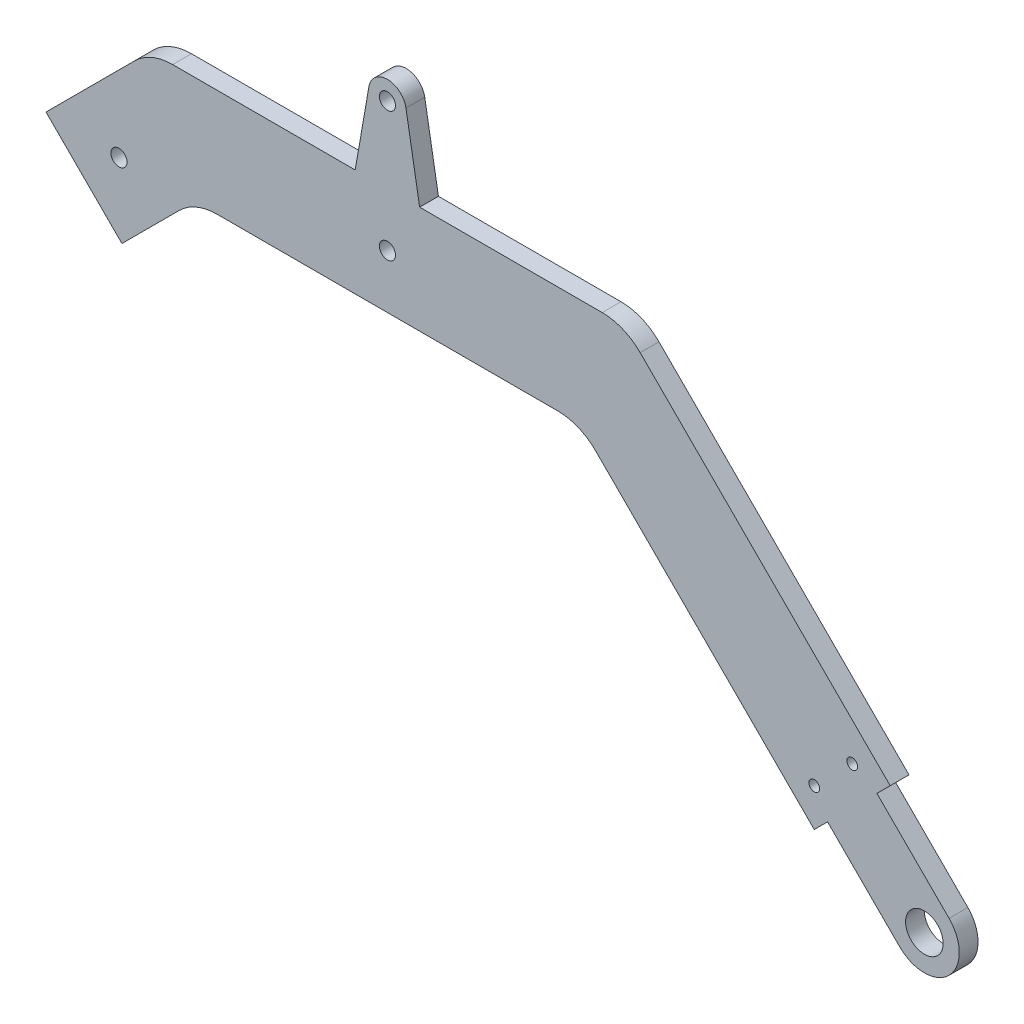
SolidWorks part; units mm, degrees
ref_plane "Front Plane" through (0, 0, 0) normal (0, 0, 1) x (1, 0, 0)
ref_plane "Top Plane" through (0, 0, 0) normal (0, 1, 0) x (1, 0, 0)
ref_plane "Right Plane" through (0, 0, 0) normal (1, 0, 0) x (0, 0, -1)
sketch "Sketch1" plane through (0, 0, 0) normal (0, 0, 1) x (1, 0, 0)
  line L0 (100, 0) -> (-100, 0)
  line L3 (-100, 0) -> (0, 100) construction
  line L4 (0, 100) -> (100, 0) construction
  line L5 (0, 0) -> (-50, 50) construction
  line L7 (0, 100) -> (0, 60) construction
  line L9 (-40, 60) -> (40, 60) construction
  circle A0 centre (-100, 0) radius 20
  circle A1 centre (0, 0) radius 20
  circle A2 centre (100, 0) radius 19.9987
  point P4 (0, 0)
  dimension "D5" = 40
  dimension "D6" = 39.9975
  dimension "D1" = 200
  dimension "D2" = 90
  dimension "D3" = 90
  dimension "D4" = 80
  dimension "D7" = 141.4214
  dimension "D8" = 70.7107
sketch "Sketch2" plane through (0, 0, 0) normal (0, 0, 1) x (1, 0, 0)
  line L0 (-56.5165, 43.4835) -> (-40, 60) construction
  line L1 (-100, 0) -> (0, 100) construction
  line L2 (-40, 60) -> (40, 60) construction
  line L3 (40, 60) -> (86.565, 13.435) construction
  line L4 (0, 100) -> (100, 0) construction
  line L5 (-49.4454, 36.4124) -> (-35.8579, 50)
  line L6 (-35.8579, 50) -> (35.8579, 50)
  line L7 (35.8579, 50) -> (79.4939, 6.364)
  line L8 (-63.5876, 50.5546) -> (-44.1421, 70)
  line L9 (-44.1421, 70) -> (44.1421, 70)
  line L10 (44.1421, 70) -> (93.636, 20.5061)
  line L11 (-63.5876, 50.5546) -> (-49.4454, 36.4124)
  line L12 (93.636, 20.5061) -> (79.4939, 6.364)
  line L13 (81.9688, 8.8388) -> (95.4038, -4.5962)
  line L14 (91.1612, 18.0312) -> (104.5962, 4.5962)
  line L15 (90.1005, 24.0416) -> (75.9584, 9.8995) construction
  line L16 (0, 100) -> (0, 60) construction
  line L17 (-6, 70) -> (-3.4486, 84.7178)
  line L18 (6, 70) -> (3.4486, 84.7178)
  circle A0 centre (100, 0) radius 3.5
  circle A1 centre (100, 0) radius 10 construction
  circle A2 centre (100, 0) radius 6.5
  circle A3 centre (79.4939, 13.435) radius 1
  circle A4 centre (86.565, 20.5061) radius 1
  circle A5 centre (0, 60) radius 1.5
  circle A6 centre (0, 84.12) radius 1.5
  circle A7 centre (0, 84.12) radius 3.5
  circle A8 centre (-50, 50) radius 1.5
  point P51 (0, 70)
  dimension "D4" = 20
  dimension "D5" = 7
  dimension "D9" = 2
  dimension "D12" = 3
  dimension "D17" = 3
  dimension "D3" = 27.5
  dimension "D7" = 19
  dimension "D8" = 5
  dimension "D10" = 5
  dimension "D11" = 5
  dimension "D13" = 14.12
  dimension "D15" = 6
  dimension "D16" = 6
  dimension "D1" = 10
  dimension "D2" = 10
  dimension "D6" = 3
  dimension "D14" = 2
sketch "Sketch3" plane through (0, 0, 0) normal (0, 0, 1) x (1, 0, 0)
  line L0 (-86.565, 13.435) -> (-50, 50) construction
  line L1 (-100, 0) -> (0, 100) construction
  line L2 (-50, 50) -> (-13.435, 13.435) construction
  line L3 (0, 0) -> (-50, 50) construction
  line L4 (-79.4939, 6.364) -> (-50, 35.8579)
  line L5 (-50, 35.8579) -> (-20.5061, 6.364)
  line L6 (-93.636, 20.5061) -> (-50, 64.1421)
  line L7 (-50, 64.1421) -> (-6.364, 20.5061)
  line L8 (-93.636, 20.5061) -> (-79.4939, 6.364) construction
  line L9 (-20.5061, 6.364) -> (-6.364, 20.5061)
  line L10 (-91.1612, 18.0312) -> (-104.5962, 4.5962)
  line L11 (-81.9688, 8.8388) -> (-95.4038, -4.5962)
  line L12 (-18.0312, 8.8388) -> (-4.5962, -4.5962)
  line L13 (-8.8388, 18.0312) -> (4.5962, 4.5962)
  line L14 (-90.1005, 24.0416) -> (-75.9584, 9.8995)
  line L15 (-9.8995, 24.0416) -> (-24.0416, 9.8995)
  circle A0 centre (-100, 0) radius 10 construction
  circle A1 centre (-100, 0) radius 3.5
  circle A2 centre (0, 0) radius 10 construction
  circle A3 centre (0, 0) radius 3.5
  circle A4 centre (-100, 0) radius 6.5
  circle A5 centre (0, 0) radius 6.5
  circle A6 centre (-86.565, 20.5061) radius 1
  circle A7 centre (-79.4939, 13.435) radius 1
  circle A8 centre (-13.435, 20.5061) radius 1
  circle A9 centre (-20.5061, 13.435) radius 1
  circle A10 centre (-50, 50) radius 1.5 construction
  circle A11 centre (-50, 50) radius 1.5
  dimension "D1" = 20
  dimension "D2" = 7
  dimension "D9" = 2
  dimension "D13" = 2
  dimension "D6" = 19
  dimension "D7" = 19
  dimension "D8" = 5
  dimension "D10" = 5
  dimension "D11" = 5
  dimension "D12" = 5
  dimension "D14" = 5
  dimension "D15" = 5
  dimension "D3" = 3
  dimension "D4" = 10
  dimension "D5" = 10
sketch "Sketch4" plane through (0, 0, 0) normal (0, 0, 1) x (1, 0, 0)
  line L6 (-57.5, 92.6154) -> (57.5, 92.6154)
  line L7 (57.5, 92.6154) -> (57.5, 82.6154)
  line L8 (57.5, 82.6154) -> (44.1421, 70)
  line L9 (44.1421, 70) -> (-44.1421, 70)
  line L10 (-44.1421, 70) -> (-57.5, 82.6154)
  line L11 (-57.5, 82.6154) -> (-57.5, 92.6154)
  line L12 (-4, 60) -> (-4, 70)
  line L13 (4, 60) -> (4, 70)
  line L14 (-22.5, 84.1154) -> (22.5, 84.1154) construction
  line L15 (-22.5, 88.6154) -> (22.5, 88.6154)
  line L16 (-22.5, 79.6154) -> (22.5, 79.6154)
  arc A1 (-22.5, 88.6154) -> (-22.5, 79.6154) centre (-22.5, 84.1154) ccw
  circle A2 centre (0, 60) radius 4
  circle A3 centre (0, 60) radius 4
  arc A4 (22.5, 79.6154) -> (22.5, 88.6154) centre (22.5, 84.1154) ccw
  point P2 (0, 92.6154)
  point P15 (0, 84.1154)
  dimension "D1" = 115
  dimension "D2" = 10
  dimension "D3" = 2.5
  dimension "D4" = 45
  dimension "D5" = 9
  dimension "D6" = 12.6154
  dimension "D7" = 4
sketch "Sketch5" plane through (0, 0, 0) normal (0, 0, 1) x (1, 0, 0)
  line L0 (91.1612, 18.0312) -> (104.5962, 4.5962) construction
  line L1 (81.9688, 8.8388) -> (95.4038, -4.5962) construction
  line L2 (6, 70) -> (3.4486, 84.7178) construction
  line L3 (-6, 70) -> (-3.4486, 84.7178) construction
  line L4 (91.1612, 18.0312) -> (104.5962, 4.5962)
  line L5 (81.9688, 8.8388) -> (95.4038, -4.5962)
  line L6 (6, 70) -> (3.4486, 84.7178)
  line L7 (-6, 70) -> (-3.4486, 84.7178)
  line L8 (93.636, 20.5061) -> (44.1421, 70)
  line L9 (79.4939, 6.364) -> (93.636, 20.5061)
  line L10 (35.8579, 50) -> (79.4939, 6.364)
  line L11 (-35.8579, 50) -> (35.8579, 50)
  line L12 (-49.4454, 36.4124) -> (-35.8579, 50)
  line L13 (-63.5876, 50.5546) -> (-49.4454, 36.4124)
  line L14 (-44.1421, 70) -> (-63.5876, 50.5546)
  line L15 (44.1421, 70) -> (-44.1421, 70)
  line L16 (93.636, 20.5061) -> (44.1421, 70)
  line L17 (79.4939, 6.364) -> (81.9688, 8.8388)
  line L18 (35.8579, 50) -> (79.4939, 6.364)
  line L19 (-35.8579, 50) -> (35.8579, 50)
  line L20 (-49.4454, 36.4124) -> (-35.8579, 50)
  line L21 (-63.5876, 50.5546) -> (-49.4454, 36.4124)
  line L22 (-44.1421, 70) -> (-63.5876, 50.5546)
  line L23 (-6, 70) -> (-44.1421, 70)
  line L24 (6, 70) -> (44.1421, 70)
  line L25 (93.636, 20.5061) -> (91.1612, 18.0312)
  arc A0 (-3.4486, 84.7178) -> (3.4486, 84.7178) centre (0, 84.12) cw
  circle A1 centre (86.565, 20.5061) radius 1
  circle A2 centre (86.565, 20.5061) radius 1
  circle A3 centre (79.4939, 13.435) radius 1
  circle A4 centre (79.4939, 13.435) radius 1
  arc A5 (104.5962, 4.5962) -> (95.4038, -4.5962) centre (100, 0) cw
  circle A7 centre (100, 0) radius 3.5
  circle A8 centre (100, 0) radius 3.5
  circle A11 centre (0, 84.12) radius 1.5
  circle A12 centre (0, 84.12) radius 1.5
  circle A13 centre (0, 60) radius 1.5
  circle A14 centre (0, 60) radius 1.5
  circle A15 centre (-50, 50) radius 1.5
  circle A16 centre (-50, 50) radius 1.5
  dimension "D1" = 0
  dimension "D2" = 0
  dimension "D4" = 0
  dimension "D5" = 0
  dimension "D7" = 0
  dimension "D8" = 0
  dimension "D9" = 0
extrude "Boss-Extrude1" add sketch "Sketch5" along normal blind 3.5
fillet "Fillet1" radius 10 4 edges at (35.8579, 50, 1.75) (-35.8579, 50, 1.75) (-44.1421, 70, 1.75) (44.1421, 70, 1.75)
